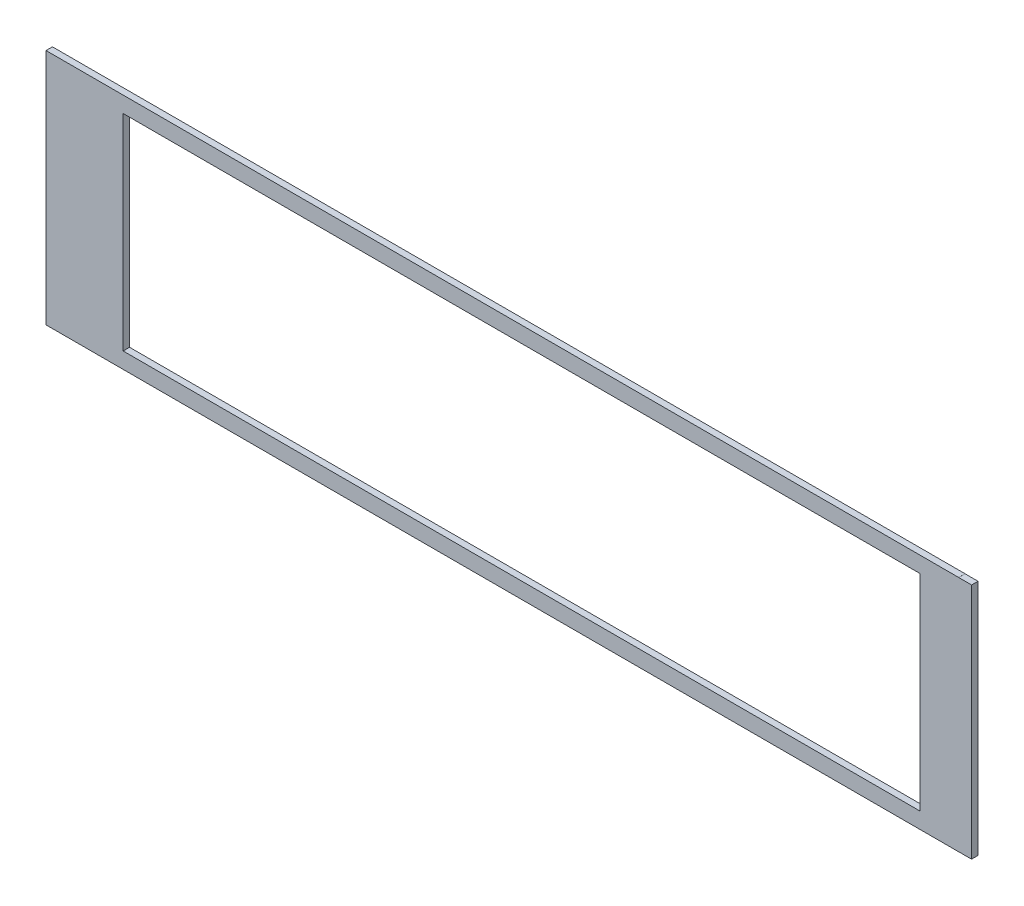
SolidWorks part; units mm, degrees
ref_plane "Front Plane" through (0, 0, 0) normal (0, 0, 1) x (1, 0, 0)
ref_plane "Top Plane" through (0, 0, 0) normal (0, 1, 0) x (1, 0, 0)
ref_plane "Right Plane" through (0, 0, 0) normal (1, 0, 0) x (0, 0, -1)
sketch "Sketch1" plane through (0, 0, 0) normal (0, 0, 1) x (1, 0, 0)
  line L0 (0, 58.6835) -> (457.2, 58.6835) construction
  line L1 (0, 0) -> (450.85, 0)
  line L2 (0, 0) -> (0, 117.3671)
  line L3 (0, 117.3671) -> (450.85, 117.3671)
  line L4 (457.2, 0) -> (457.2, 117.3671)
  line L6 (450.85, 117.3671) -> (450.85, 117.3416)
  line L7 (450.85, 117.3416) -> (457.2, 117.3416)
  line L8 (457.2, 117.3671) -> (457.2, 117.3416)
  line L9 (457.2, 0) -> (457.2, 0.0254)
  line L10 (450.85, 0.0254) -> (457.2, 0.0254)
  line L11 (450.85, 0) -> (450.85, 0.0254)
  line L13 (38.1, 109.4835) -> (431.8, 109.4835)
  line L14 (38.1, 109.4835) -> (38.1, 7.8835)
  line L15 (38.1, 7.8835) -> (431.8, 7.8835)
  line L16 (431.8, 109.4835) -> (431.8, 7.8835)
  point P17 (38.1, 58.6835)
  dimension "D1" = 457.2
  dimension "D2" = 117.3671
  dimension "D3" = 117.3162
  dimension "D4" = 6.35
  dimension "D5" = 25.4
  dimension "D7" = 101.6
  dimension "D6" = 393.7
extrude "Boss-Extrude1" add sketch "Sketch1" along normal blind 3.175 contours L0 L2 L1 L11 L10 L4 L16 L15 L14 | L2 L0 L14 L13 L16 L4 L7 L6 L3
equation "\"ROADWIDTH\" = 4.62075"
equation "\"TABWIDTH\" = 4.61875"
equation "\"D2@Sketch1\"=\"ROADWIDTH\""
equation "\"D3@Sketch1\"=\"TABWIDTH\""
